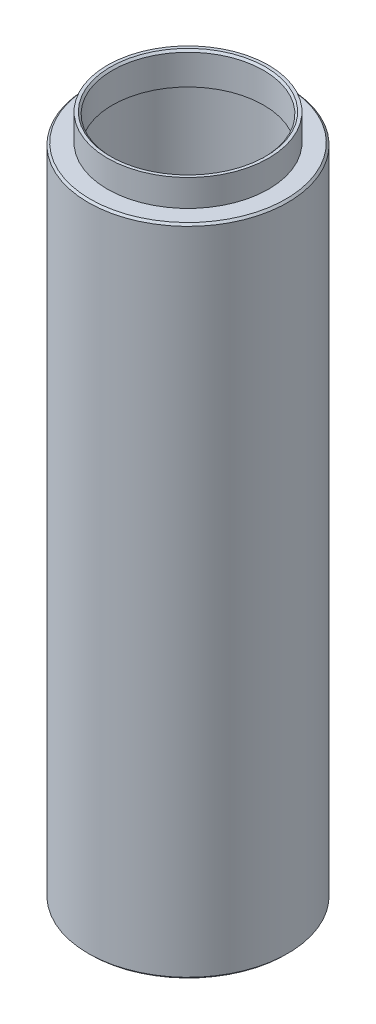
SolidWorks part; units mm, degrees
ref_plane "Front Plane" through (0, 0, 0) normal (0, 0, 1) x (1, 0, 0)
ref_plane "Top Plane" through (0, 0, 0) normal (0, 1, 0) x (1, 0, 0)
ref_plane "Right Plane" through (0, 0, 0) normal (1, 0, 0) x (0, 0, -1)
sketch "Sketch1" plane through (0, 0, 0) normal (0, 0, 1) x (1, 0, 0)
  line L0 (0, 0) -> (0, 104.1) construction
  line L1 (12.7, 0) -> (12.7, 98.552)
  line L2 (12.7, 98.552) -> (13.208, 98.552)
  line L3 (13.208, 98.552) -> (13.208, 99.2)
  line L4 (13.208, 99.2) -> (11.557, 99.2)
  line L5 (11.557, 99.2) -> (11.557, 103.8)
  line L6 (11.857, 104.1) -> (12.319, 104.1)
  line L7 (12.319, 104.1) -> (12.319, 100)
  line L8 (12.319, 100) -> (14.95, 100)
  line L9 (15.25, 99.7) -> (15.25, 0.3)
  line L10 (14.95, 0) -> (12.7, 0)
  line L11 (15.25, 0.3) -> (14.95, 0)
  line L12 (14.95, 100) -> (15.25, 99.7)
  line L13 (11.557, 103.8) -> (11.857, 104.1)
  point P9 (11.557, 104.1)
  point P12 (15.25, 100)
  point P13 (15.25, 0)
  dimension "D1" = 104.1
  dimension "D2" = 100
  dimension "D3" = 99.2
  dimension "D4" = 30.5
  dimension "D5" = 25.4
  dimension "D6" = 98.552
  dimension "D7" = 0.508
  dimension "D8" = 23.114
  dimension "D9" = 0.762
revolve "Revolve1" add sketch "Sketch1" angle 360 about L0
thread "Thread1" pitch 0.3175 start angle 0, offset 0, length 3.302, pitch 0.794, diameter 24.638
ref_plane "Plane2" through (-12.319, 104.1, 0) normal (0, 0, 1) x (-1, 0, 0)
sketch "Thread Profile2" plane through (-12.319, 104.1, 0) normal (0, 0, 1) x (-1, 0, 0)
  line L0 (0, 0) -> (0, 0.3175) construction
  line L1 (0, 0) -> (0.1719, 0.0992)
  line L2 (0.1719, 0.0992) -> (0.1719, 0.1389)
  line L3 (0.1719, 0.1389) -> (0, 0.2381)
  line L4 (0.1719, 0.1191) -> (0, 0.1191) construction
  line L11 (0, 0) -> (0, 0.2381)
  point P2 (0, 0)
  dimension "Pitch" = 0.3175
  dimension "Profile_Angle" = 60
  dimension "Profile_Land" = 0.0397
  dimension "Profile_Height" = 0.1719
thread "Thread2" pitch 0.3175 start angle 0, offset 0, length 0, pitch 0.794, diameter 25.4
ref_plane "Plane3" through (12.7, 0, 0) normal (0, 0, 1) x (1, 0, 0)
sketch "Thread Profile3" plane through (12.7, 0, 0) normal (0, 0, 1) x (1, 0, 0)
  line L0 (0, 0) -> (0, 0.3175) construction
  line L1 (0, 0) -> (0.1719, 0.0992)
  line L2 (0.1719, 0.0992) -> (0.1719, 0.1389)
  line L3 (0.1719, 0.1389) -> (0, 0.2381)
  line L4 (0.1719, 0.1191) -> (0, 0.1191) construction
  line L11 (0, 0) -> (0, 0.2381)
  point P2 (0, 0)
  dimension "Pitch" = 0.3175
  dimension "Profile_Angle" = 60
  dimension "Profile_Land" = 0.0397
  dimension "Profile_Height" = 0.1719
